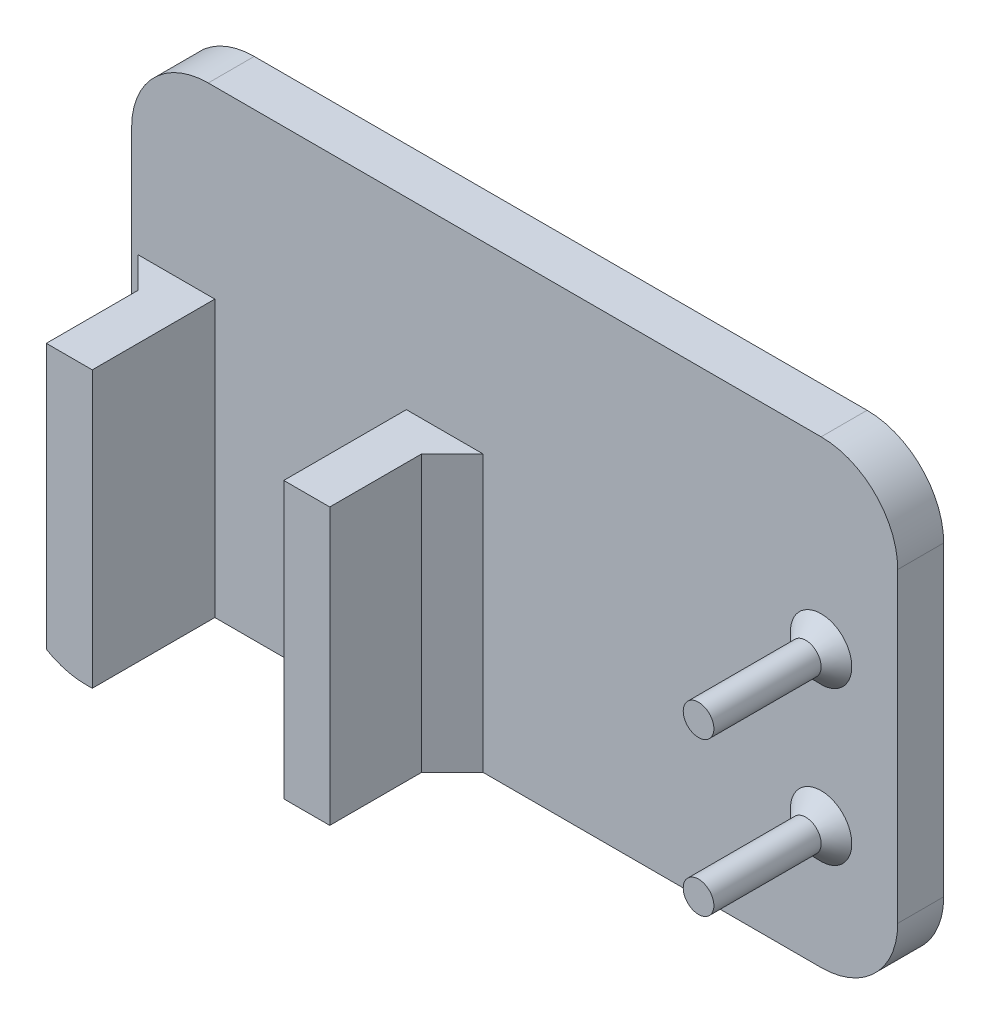
SolidWorks part; units mm, degrees
ref_plane "Front Plane" through (0, 0, 0) normal (0, 0, 1) x (1, 0, 0)
ref_plane "Top Plane" through (0, 0, 0) normal (0, 1, 0) x (1, 0, 0)
ref_plane "Right Plane" through (0, 0, 0) normal (1, 0, 0) x (0, 0, -1)
sketch "Sketch1" plane through (0, 0, 0) normal (0, 0, 1) x (1, 0, 0)
  line L1 (0, 0) -> (50, 0)
  line L2 (0, 0) -> (0, 30)
  line L3 (0, 30) -> (50, 30)
  line L4 (50, 0) -> (50, 30)
  dimension "D1" = 30
  dimension "D2" = 50
extrude "Boss-Extrude1" add sketch "Sketch1" along normal blind 3
sketch "Sketch2" plane through (0, 0, 3) normal (0, 0, 1) x (1, 0, 0)
  line L0 (2.4305, 18) -> (2.4305, 0)
  line L2 (5.4305, 18) -> (5.4305, 0)
  line L4 (17.9305, 18) -> (17.9305, 0)
  line L6 (20.9305, 18) -> (20.9305, 0)
  line L8 (5.4305, 18) -> (2.4305, 18)
  line L9 (17.9305, 18) -> (20.9305, 18)
  line L10 (2.4305, 21) -> (2.4305, -4.9123) construction
  line L11 (2.4305, 21) -> (20.9305, 21) construction
  line L12 (20.9305, 21) -> (20.9305, -4.9123) construction
  line L13 (5.4305, 18) -> (17.9305, 18) construction
  line L14 (5.4305, -1.9123) -> (17.9305, -1.9123) construction
  line L15 (2.4305, -4.9123) -> (20.9305, -4.9123) construction
  line L16 (5.4305, 18) -> (5.4305, -1.9123) construction
  line L17 (17.9305, 18) -> (17.9305, -1.9123) construction
  line L20 (0, 30) -> (0, 0)
  line L21 (0, 0) -> (50, 0)
  line L22 (50, 0) -> (50, 30)
  line L23 (50, 30) -> (0, 30)
  line L24 (0, 30) -> (0, 0)
  line L25 (0, 0) -> (50, 0)
  line L26 (50, 0) -> (50, 30)
  line L27 (50, 30) -> (0, 30)
  circle A0 centre (45, 18) radius 1
  circle A1 centre (45, 8) radius 1
  point P22 (0, 0)
  point P23 (0, 0)
  line M7 (0, 0) -> (50, 0)
  dimension "D5" = 2
  dimension "D6" = 2
  dimension "D1" = 18
  dimension "D2" = 12.5
  dimension "D4" = 0
  dimension "D7" = 10
  dimension "D8" = 5
  dimension "D9" = 8
  dimension "D3" = 3
extrude "Boss-Extrude2" add sketch "Sketch2" along normal blind 8 contours L2 L8 L0 M7 | L9 L4 L6 M7 | A0 | A1
chamfer "Chamfer1" distance 2 angle 45 2 edges at (20.9305, 9, 3) (2.4305, 9, 3)
fillet "Fillet1" radius 5 4 edges at (0, 0, 1.5) (50, 0, 1.5) (50, 30, 1.5) (0, 30, 1.5)
chamfer "Chamfer3" distance 1 angle 45 2 edges at (44, 18, 3) (44, 8, 3)
